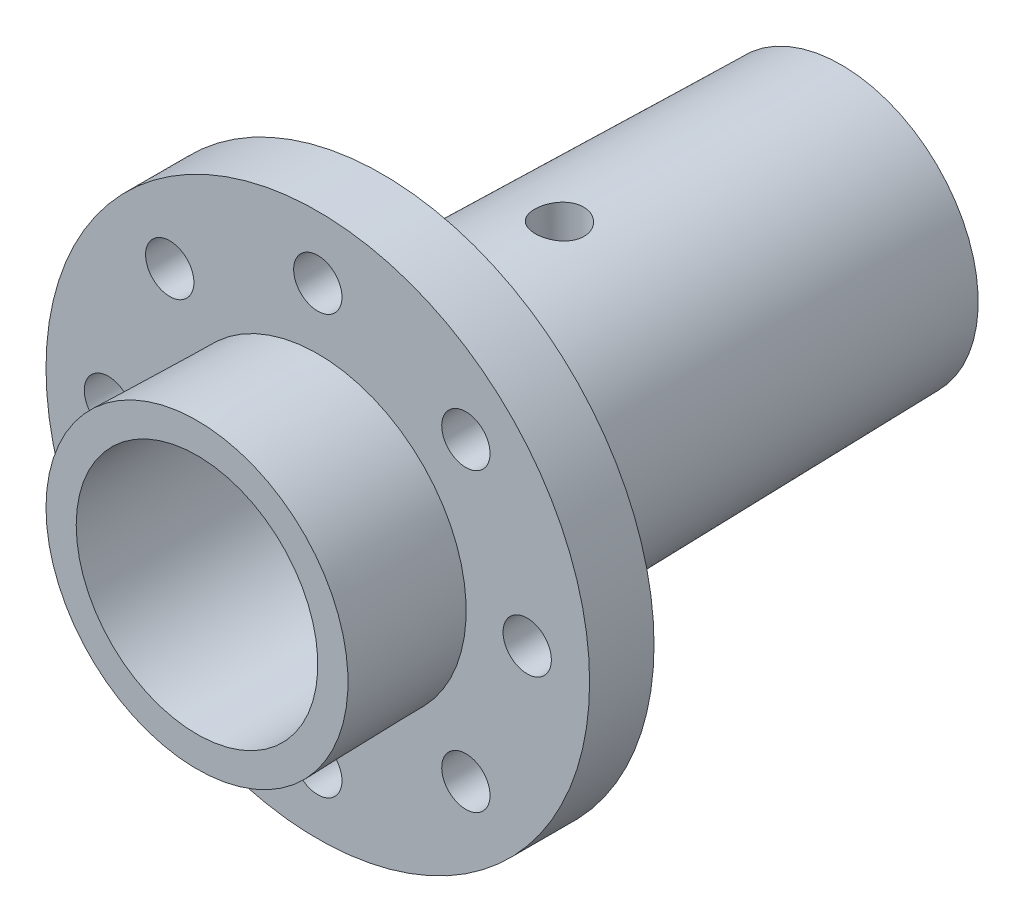
SolidWorks part; units mm, degrees
ref_plane "Piano frontale" through (0, 0, 0) normal (0, 0, 1) x (1, 0, 0)
ref_plane "Piano superiore" through (0, 0, 0) normal (0, 1, 0) x (1, 0, 0)
ref_plane "Piano destro" through (0, 0, 0) normal (1, 0, 0) x (0, 0, -1)
sketch "Schizzo3" plane through (0, 0, 0) normal (0, 1, 0) x (1, 0, 0)
  line L0 (-17, 40) -> (-12, 40)
  line L1 (-12, 40) -> (-12, -40)
  line L2 (-12, -40) -> (-18.75, -40)
  line L3 (-18.75, -40) -> (-18.4219, -25)
  line L4 (-18.4219, -25) -> (-33.75, -25)
  line L5 (-33.75, -25) -> (-33.75, -17)
  line L6 (-33.75, -17) -> (-18.2469, -17)
  line L7 (-18.2469, -17) -> (-17, 40)
  line L12 (0, -55) -> (0, 55) construction
  line L14 (-55, 0) -> (55, 0) construction
  line L15 (0, 65.0811) -> (0, -61.5974) construction
  point P6 (-19.2187, -40)
  dimension "D1" = 18.75
  dimension "D2" = 5
  dimension "D3" = 15
  dimension "D4" = 12
  dimension "D5" = 8
  dimension "D6" = 57
  dimension "D7" = 33.75
  dimension "D8" = 40
revolve "Rivoluzione2" add sketch "Schizzo3" angle 360 about L15
sketch "Schizzo5" plane through (0, 0, 0) normal (0, 1, 0) x (1, 0, 0)
  line L0 (-15, -40) -> (-15, -10)
  line L1 (-18.75, -40) -> (18.75, -40) construction
  line L2 (-15, -10) -> (0, -10)
  line L3 (0, -37.125) -> (0, 37.125) construction
  line L4 (0, -10) -> (0, -40)
  line L5 (0, -40) -> (-15, -40)
  line L6 (0, 67.5584) -> (0, -85.5937) construction
  point P11 (0, 0)
  dimension "D1" = 30
  dimension "D2" = 15
revolve "Taglia-Rivoluzione1" cut sketch "Schizzo5" angle 360 about L6
sketch "Schizzo7" plane through (0, 0, 17) normal (0, 0, -1) x (-1, 0, 0)
  circle A0 centre (0, 0) radius 26 construction
  circle A1 centre (0, -26) radius 3
  dimension "D1" = 52
  dimension "D2" = 6
extrude "Taglio-Estrusione1" cut sketch "Schizzo7" against normal through all
pattern_circular "RipetizioneCircolare1" count 8 over 360 about axis through (0, 0, 0) along (0, 0, 1) of "Taglio-Estrusione1"
sketch "Schizzo8" plane through (0, 0, 0) normal (0, 1, 0) x (1, 0, 0)
  line L0 (0, -37.125) -> (0, 37.125) construction
  line L1 (17, 40) -> (-17, 40) construction
  circle A0 centre (0, 5) radius 3
  dimension "D1" = 6
  dimension "D2" = 35
extrude "Taglio-Estrusione2" cut sketch "Schizzo8" along normal through all
